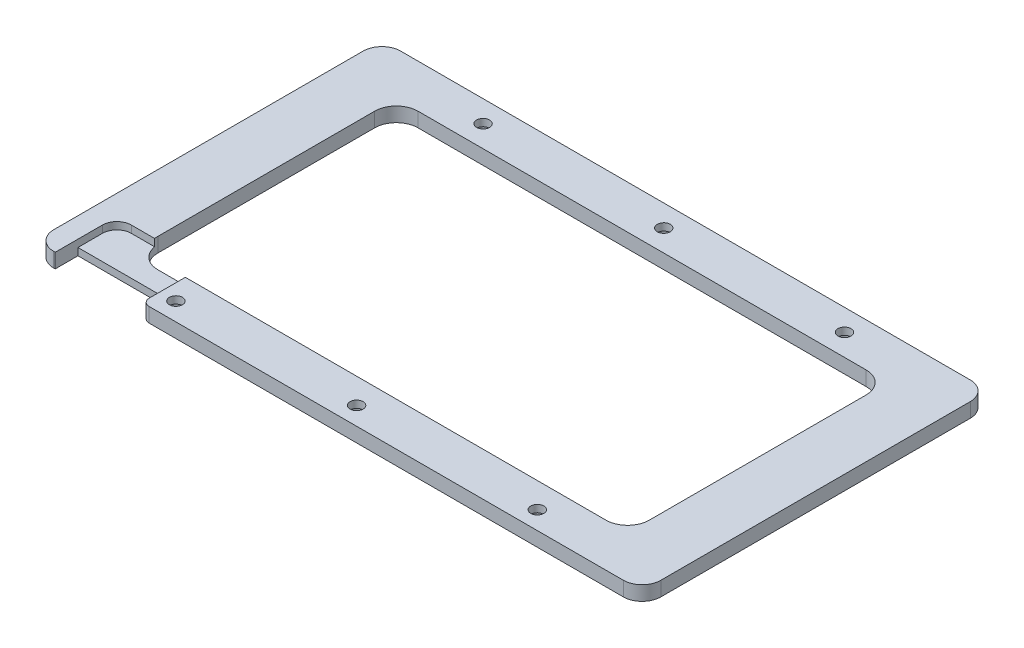
SolidWorks part; units mm, degrees
ref_plane "前视基准面" through (0, 0, 0) normal (0, 0, 1) x (1, 0, 0)
ref_plane "上视基准面" through (0, 0, 0) normal (0, 1, 0) x (1, 0, 0)
ref_plane "右视基准面" through (0, 0, 0) normal (1, 0, 0) x (0, 0, -1)
other "Configuration Table"
sketch "草图1" plane through (0, 0, 0) normal (0, 1, 0) x (1, 0, 0)
  line L0 (-39.4076, 24.2574) -> (39.3978, 24.2574)
  line L1 (-42.0049, 21.6601) -> (-42.0049, -21.1453)
  line L2 (-39.4076, -23.7426) -> (39.3978, -23.7426)
  line L3 (41.9951, 21.6601) -> (41.9951, -21.1453)
  line L4 (-40.0049, 24.2574) -> (39.9951, -23.7426) construction
  line L5 (-40.0049, -23.7426) -> (39.9951, 24.2574) construction
  line L6 (-31.0049, 18.2574) -> (30.9951, 18.2574)
  line L7 (-34.0049, 15.2574) -> (-34.0049, -14.7426)
  line L8 (-31.0049, -17.7426) -> (30.9951, -17.7426)
  line L9 (33.9951, 15.2574) -> (33.9951, -14.7426)
  line L10 (-34.0049, 18.2574) -> (33.9951, -17.7426) construction
  line L11 (-34.0049, -17.7426) -> (33.9951, 18.2574) construction
  arc A0 (-34.0049, -14.7426) -> (-31.0049, -17.7426) centre (-31.0049, -14.7426) ccw
  arc A1 (30.9951, -17.7426) -> (33.9951, -14.7426) centre (30.9951, -14.7426) ccw
  arc A2 (33.9951, 15.2574) -> (30.9951, 18.2574) centre (30.9951, 15.2574) ccw
  arc A3 (-31.0049, 18.2574) -> (-34.0049, 15.2574) centre (-31.0049, 15.2574) ccw
  arc A4 (-42.0049, -21.1453) -> (-39.4076, -23.7426) centre (-39.4076, -21.1453) ccw
  arc A5 (39.3978, -23.7426) -> (41.9951, -21.1453) centre (39.3978, -21.1453) ccw
  arc A6 (41.9951, 21.6601) -> (39.3978, 24.2574) centre (39.3978, 21.6601) ccw
  arc A7 (-39.4076, 24.2574) -> (-42.0049, 21.6601) centre (-39.4076, 21.6601) ccw
  circle A8 centre (-25.0049, 21.2574) radius 0.9
  circle A9 centre (-0.0049, 21.2574) radius 0.9
  circle A10 centre (24.9951, 21.2574) radius 0.9
  circle A11 centre (24.9951, -21.2426) radius 0.9
  circle A12 centre (-0.0049, -21.2426) radius 0.9
  circle A13 centre (-25.0049, -21.2426) radius 0.9
  point P0 (-0.0049, 0.2574)
  point P22 (-0.0049, 0.2574)
  point P46 (0, 0)
  dimension "D4" = 2.5973
  dimension "D5" = 1.8
  dimension "D6" = 1.8
  dimension "D7" = 1.8
  dimension "D8" = 1.8
  dimension "D9" = 1.8
  dimension "D10" = 1.8
  dimension "D13" = 3
  dimension "D1" = 48
  dimension "D2" = 36
  dimension "D3" = 68
  dimension "D11" = 42
  dimension "D12" = 42
extrude "凸台-拉伸1" add sketch "草图1" along normal blind 2
sketch "草图8" plane through (0, 2, 0) normal (0, 1, 0) x (1, 0, 0)
  line L1 (-39.2, -15.2149) -> (-27.2, -15.2149)
  line L2 (-39.2, -15.2149) -> (-39.2, -25.2417)
  line L3 (-39.2, -25.2417) -> (-27.2, -25.2417)
  line L4 (-27.2, -15.2149) -> (-27.2, -25.2417)
  line L5 (-39.2, -15.2149) -> (-27.2, -25.2417) construction
  line L6 (-39.2, -25.2417) -> (-27.2, -15.2149) construction
  point P0 (-33.2, -20.2283)
  dimension "D1" = 12
  dimension "D2" = 33.2
extrude "切除-拉伸4" cut sketch "草图8" against normal blind 1
sketch "草图9" plane through (0, 0, 0) normal (0, -1, 0) x (1, 0, 0)
  circle A0 centre (-25.0049, 21.2426) radius 1.5
  circle A1 centre (-0.0049, 21.2426) radius 1.5
  circle A2 centre (24.9951, 21.2426) radius 1.5
  circle A3 centre (-25.0049, -21.2574) radius 1.5
  circle A4 centre (-0.0049, -21.2574) radius 1.5
  circle A5 centre (24.9951, -21.2574) radius 1.5
  dimension "D1" = 3
  dimension "D2" = 3
  dimension "D3" = 3
  dimension "D4" = 3
  dimension "D5" = 3
  dimension "D6" = 3
extrude "切除-拉伸7" cut sketch "草图9" against normal blind 1
fillet "圆角1" radius 2 1 edges at (-39.2, 1.5, 15.2149)
sketch "草图10" plane through (0, 1, 0) normal (0, 1, 0) x (1, 0, 0)
  line L0 (-39.2, -23.7426) -> (-27.2, -23.7426) construction
  line L1 (-39.2, -20.6013) -> (-27.2, -20.6013)
  line L2 (-39.2, -20.6013) -> (-39.2, -26.884)
  line L3 (-39.2, -26.884) -> (-27.2, -26.884)
  line L4 (-27.2, -20.6013) -> (-27.2, -26.884)
  line L5 (-39.2, -20.6013) -> (-27.2, -26.884) construction
  line L6 (-39.2, -26.884) -> (-27.2, -20.6013) construction
  point P0 (-33.2, -23.7426)
extrude "切除-拉伸8" cut sketch "草图10" against normal through all
fillet "圆角2" radius 1 1 edges at (-27.2, 1, 23.7426)
